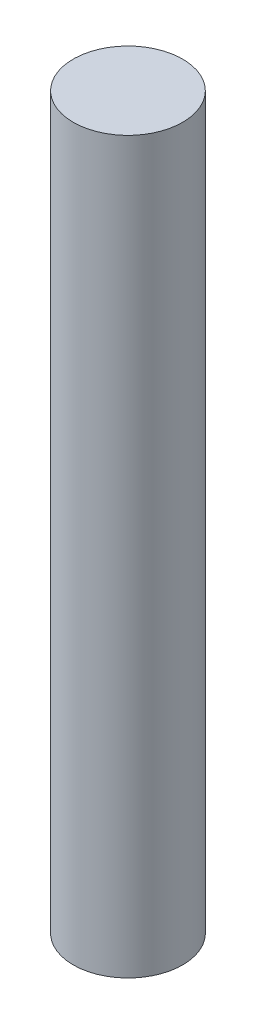
SolidWorks part; units mm, degrees
material "AISI 1020"
ref_plane "Front Plane" through (0, 0, 0) normal (0, 0, 1) x (1, 0, 0)
ref_plane "Top Plane" through (0, 0, 0) normal (0, 1, 0) x (1, 0, 0)
ref_plane "Right Plane" through (0, 0, 0) normal (1, 0, 0) x (0, 0, -1)
sketch "Sketch2" plane through (0, 0, 0) normal (0, 1, 0) x (1, 0, 0)
  circle A0 centre (0, 0) radius 3
  dimension "D1" = 6
extrude "Boss-Extrude1" add sketch "Sketch2" along normal blind 40
